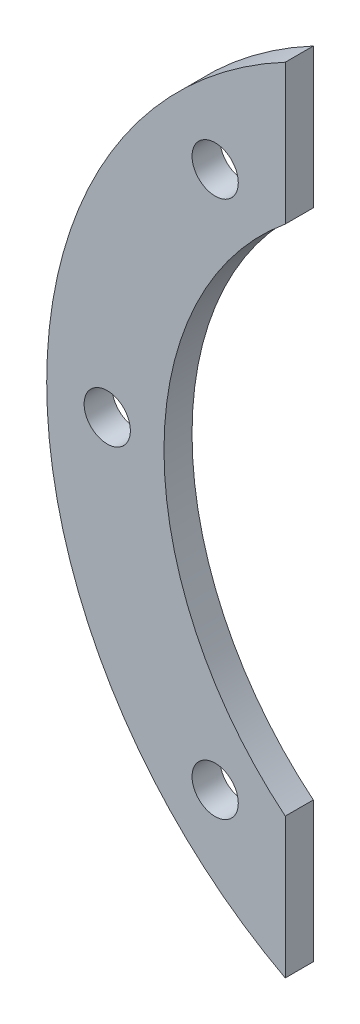
SolidWorks part; units mm, degrees
ref_plane "前视基准面" through (0, 0, 0) normal (0, 0, 1) x (1, 0, 0)
ref_plane "上视基准面" through (0, 0, 0) normal (0, 1, 0) x (1, 0, 0)
ref_plane "右视基准面" through (0, 0, 0) normal (1, 0, 0) x (0, 0, -1)
sketch "草图1" plane through (0, 0, 0) normal (0, 0, 1) x (1, 0, 0)
  line L0 (10, 68.2843) -> (10, 78.2843)
  line L1 (0, 0) -> (10, 0)
  line L2 (0, 0) -> (0, 30)
  line L4 (10, 0) -> (10, 31.7157)
  arc A0 (10, 68.2843) -> (10, 31.7157) centre (25, 50) ccw
  arc A1 (10, 78.2843) -> (0, 30) centre (25, 50) ccw
  circle A2 centre (5, 5) radius 1.65
  circle A3 centre (5, 17) radius 1.65
  arc A4 (10, 73.2843) -> (10, 26.7157) centre (25, 50) ccw construction
  circle A5 centre (-2.6976, 50) radius 1.65
  circle A6 centre (5, 69.1613) radius 1.65
  circle A7 centre (5, 30.8387) radius 1.65
  point P12 (10, 73.2843)
  point P25 (5, 0)
  dimension "D6" = 3.3
  dimension "D7" = 3.3
  dimension "D10" = 3.3
  dimension "D11" = 3.3
  dimension "D12" = 3.3
  dimension "D1" = 10
  dimension "D2" = 30
  dimension "D3" = 15
  dimension "D4" = 50
  dimension "D5" = 12
  dimension "D8" = 5
  dimension "D9" = 10
  dimension "D13" = 5
extrude "凸台-拉伸1" add sketch "草图1" along normal blind 2
sketch "草图2" plane through (0, 0, 2) normal (0, 0, 1) x (1, 0, 0)
  circle A0 centre (25, 50) radius 32.0156
extrude "切除-拉伸1" cut sketch "草图2" against normal blind 10 flip side to cut
